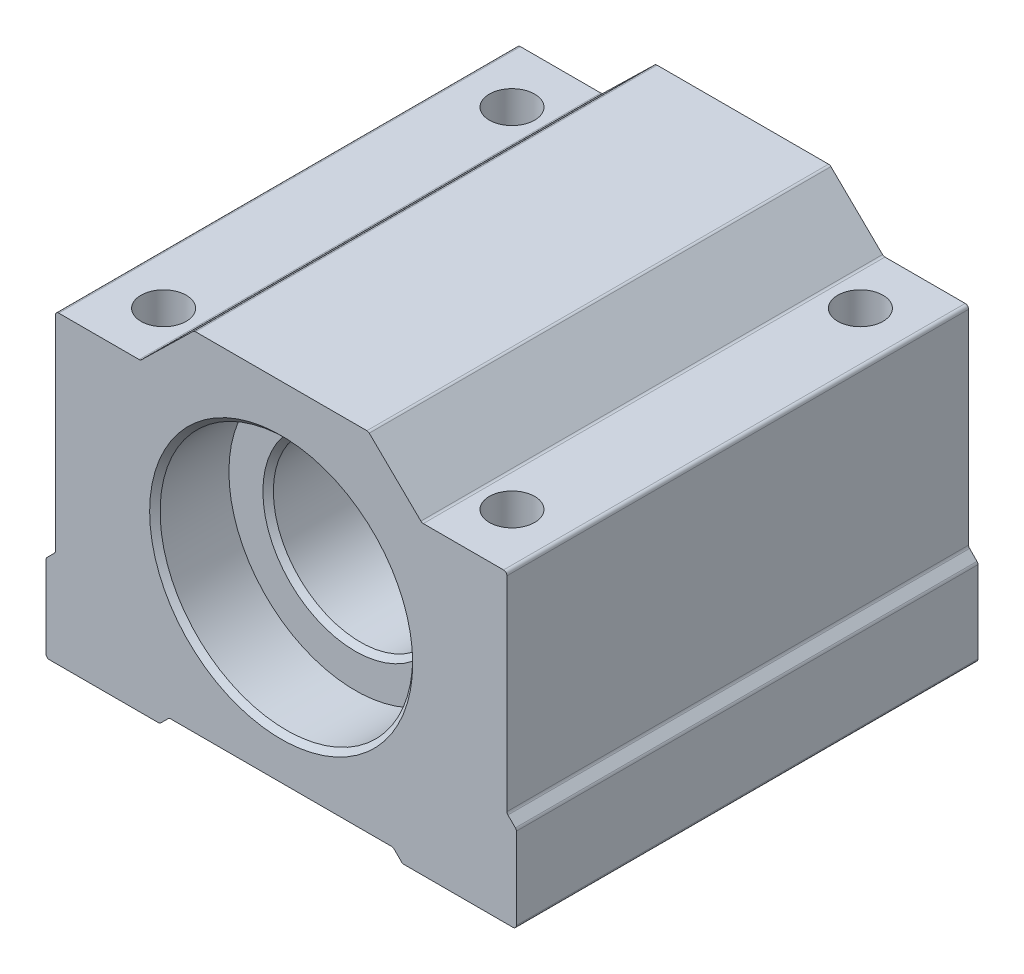
SolidWorks part; units mm, degrees
ref_plane "Front Plane" through (0, 0, 0) normal (0, 0, 1) x (1, 0, 0)
ref_plane "Top Plane" through (0, 0, 0) normal (0, 1, 0) x (1, 0, 0)
ref_plane "Right Plane" through (0, 0, 0) normal (1, 0, 0) x (0, 0, -1)
sketch "Sketch1" plane through (0, 0, 0) normal (0, 0, 1) x (1, 0, 0)
  line L0 (-27, -20.5) -> (27, -20.5) construction
  line L2 (0, -20.5) -> (0, 20.5) construction
  line L3 (0, -56.1) -> (0, 56.1) construction
  line L5 (-10, 0) -> (10, 0) construction
  line L6 (-22.6, 20.5) -> (-17.4, 20.5) construction
  line L7 (-20, 20.5) -> (20, 20.5) construction
  line L9 (-27, -20.5) -> (-27, 14.5) construction
  point P3 (-27, -9.5)
  point P6 (0, 0)
  point P14 (27, -20.5)
  point P20 (10, 0)
  point P22 (0, 0)
  point P23 (20, 20.5)
  point P26 (0, 20.5)
  point P28 (0, 0.5)
  point P29 (-10, 0)
  dimension "OverallWidth" = 54
  dimension "OverallHeight" = 41
  dimension "Mnting Holes CtoC Width" = 40
  dimension "SecondHeight" = 35
  dimension "BaseThickness" = 11
  dimension "Mnting Hole Dia" = 5.2
  dimension "CenterHeight" = 21
sketch "Sketch13" plane through (0, 0, 0) normal (1, 0, 0) x (0, 0, -1)
  line L0 (-26.5, 0) -> (26.5, 0) construction
  line L1 (0, 0) -> (0, 20.5) construction
  line L2 (0, -20.5) -> (0, 14.5) construction
  line L3 (0, -20.5) -> (0, 20.5) construction
  point P3 (-20, 0)
  point P12 (26.5, -20.5)
  point P14 (0, -20.5)
  point P17 (26.5, 20.5)
  dimension "OverallLength" = 53
  dimension "Mnting Holes CtoC Length" = 40
  dimension "D1" = 41
sketch "Sketch2" plane through (0, 0, 0) normal (0, 0, 1) x (1, 0, 0)
  line L0 (-27, -20.5) -> (-13.9316, -20.5)
  line L1 (-27, -20.5) -> (27, -20.5) construction
  line L2 (-13.9316, -20.5) -> (-12.8516, -19.42)
  line L3 (-12.8516, -19.42) -> (12.8516, -19.42)
  line L4 (12.8516, -19.42) -> (13.9316, -20.5)
  line L5 (13.9316, -20.5) -> (27, -20.5)
  line L6 (27, -20.5) -> (27, -10.58)
  line L8 (27, -10.58) -> (25.92, -9.5)
  line L9 (25.92, -9.5) -> (25.92, 14.5)
  line L10 (25.92, 14.5) -> (16.1538, 14.5)
  line L11 (16.1538, 14.5) -> (10, 20.5)
  line L12 (-20, 20.5) -> (20, 20.5) construction
  line L13 (10, 20.5) -> (-10, 20.5)
  line L14 (-10, 20.5) -> (-16.1538, 14.5)
  line L15 (-16.1538, 14.5) -> (-25.92, 14.5)
  line L16 (-25.92, 14.5) -> (-25.92, -9.5)
  line L17 (-25.92, -9.5) -> (-27, -10.58)
  line L18 (-27, -20.5) -> (-27, 14.5) construction
  line L19 (-27, -10.58) -> (-27, -20.5)
  line L20 (0, -20.5) -> (0, 20.5) construction
  circle A0 centre (0, 0) radius 10
  point P28 (0, -19.42)
  point P33 (0, 20.5)
  dimension "D1" = 1.08
  dimension "D3" = 1.08
  dimension "D8" = 2.2222
  dimension "D9" = 20
  dimension "D10" = 6.1538
  dimension "D11" = 6.1538
  dimension "D6" = 45
  dimension "D2" = 45
extrude "Boss-Extrude1" add sketch "Sketch2" along normal mid plane 53
sketch "Sketch3" plane through (0, 0, 0) normal (0, 1, 0) x (1, 0, 0)
  line L0 (-20, 20) -> (20, 20) construction
  line L1 (0, -56.1) -> (0, 56.1) construction
  line L2 (-20, 0) -> (20, 0) construction
  line L3 (20, 20) -> (20, -20) construction
  line L4 (-56.1, 0) -> (56.1, 0) construction
  circle A0 centre (-20, 20) radius 2.6
  circle A1 centre (20, 20) radius 2.6
  circle A2 centre (20, -20) radius 2.6
  circle A3 centre (-20, -20) radius 2.6
  point P8 (0, 20)
  point P13 (20, 0)
  dimension "D1" = 5.2
  dimension "D2" = 40
extrude "Cut-Extrude1" cut sketch "Sketch3" along normal through all both and the other way through all
sketch "Sketch12" plane through (0, 0, -26.5) normal (0, 0, -1) x (-1, 0, 0)
  circle A0 centre (0, 0) radius 10 construction
  circle A1 centre (0, 0) radius 10 construction
  circle A2 centre (0, 0) radius 14.5
  dimension "D1" = 4.5
extrude "Cut-Extrude9" cut sketch "Sketch12" against normal blind 8.5
mirror "Mirror1" about plane through (0, 0, 0) normal (0, 0, 1) of "Cut-Extrude9"
chamfer "Chamfer1" distance 0.6 angle 45 4 edges at (-14.5, 0, -26.5) (-14.5, 0, 26.5) (-10, 0, -18) (10, 0, 18)
fillet "Fillet1" radius 0.39 16 edges at (25.92, -9.5, 0) (27, -10.58, 0) (27, -20.5, 0) (13.9316, -20.5, 0) (12.8516, -19.42, 0) (-12.8516, -19.42, 0) (-13.9316, -20.5, 0) (-27, -20.5, 0) (-27, -10.58, 0) (-25.92, -9.5, 0) (-25.92, 14.5, 0) (-16.1538, 14.5, 0) (-10, 20.5, 0) (25.92, 14.5, 0) (10, 20.5, 0) (16.1538, 14.5, 0)
equation "\"D9@Sketch2\"=\"ForShaftDia@Sketch1\""
equation "\"D1@Boss-Extrude1\"=\"OverallLength@Sketch13\""
equation "\"D1@Sketch3\" = \"Mnting Hole Dia@Sketch1\""
equation "\"D2@Sketch3\"=\"Mnting Holes CtoC Length@Sketch13\""
equation "\"D1@Cut-Extrude9\"=( \"OverallLength@Sketch13\" - \"Mnting Holes CtoC Length@Sketch13\" )  / 2 + 2mm"
equation "\"D8@Sketch2\"=\"D9@Sketch2\"/9"
equation "\"D10@Sketch2\"=\"D9@Sketch2\"/3.25"
equation "\"D11@Sketch2\"=\"D10@Sketch2\""
equation "\"D1@Sketch2\"=\"OverallWidth@Sketch1\"*0.02"
equation "\"D3@Sketch2\"=\"D1@Sketch2\""
equation "\"D1@Chamfer1\"=\"ForShaftDia@Sketch1\" * 0.03"
equation "\"D1@Fillet1\" = \"Mnting Hole Dia@Sketch1\" * 0.075"
